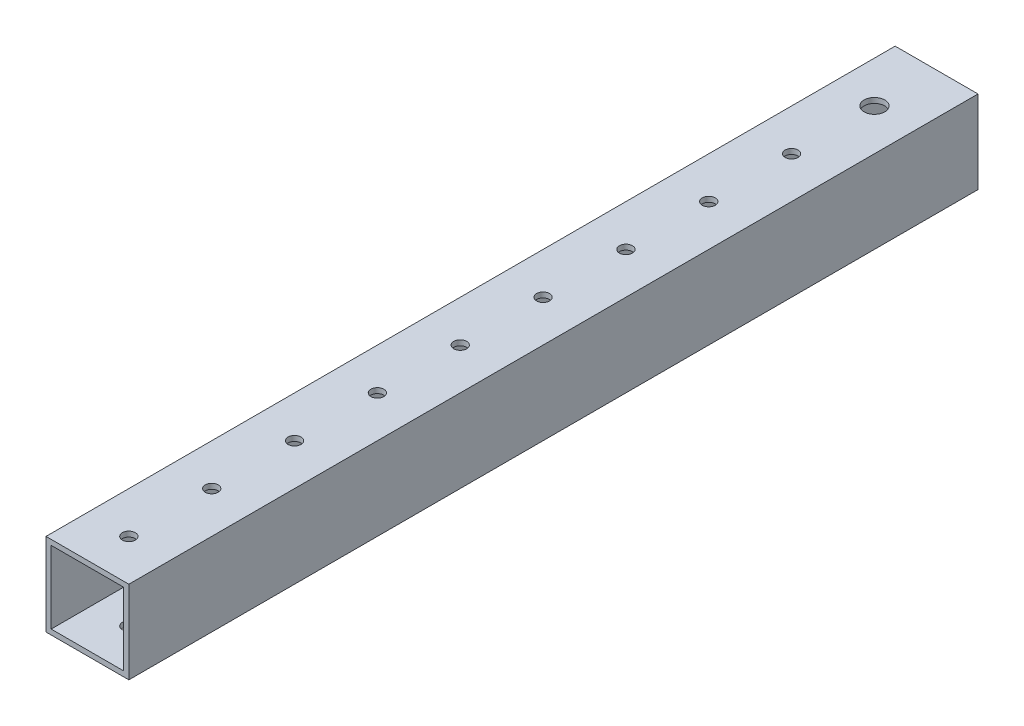
SolidWorks part; units mm, degrees
ref_plane "Front Plane" through (0, 0, 0) normal (0, 0, 1) x (1, 0, 0)
ref_plane "Top Plane" through (0, 0, 0) normal (0, 1, 0) x (1, 0, 0)
ref_plane "Right Plane" through (0, 0, 0) normal (1, 0, 0) x (0, 0, -1)
sketch "Sketch1" plane through (0, 0, 0) normal (0, 0, 1) x (1, 0, 0)
  line L1 (-11.1125, 11.1125) -> (11.1125, 11.1125)
  line L2 (-11.1125, 11.1125) -> (-11.1125, -11.1125)
  line L3 (-11.1125, -11.1125) -> (11.1125, -11.1125)
  line L4 (11.1125, 11.1125) -> (11.1125, -11.1125)
  line L5 (-11.1125, 11.1125) -> (11.1125, -11.1125) construction
  line L6 (-11.1125, -11.1125) -> (11.1125, 11.1125) construction
  line L7 (-12.7, 12.7) -> (12.7, 12.7)
  line L8 (-12.7, 12.7) -> (-12.7, -12.7)
  line L9 (-12.7, -12.7) -> (12.7, -12.7)
  line L10 (12.7, 12.7) -> (12.7, -12.7)
  line L11 (-12.7, 12.7) -> (12.7, -12.7) construction
  line L12 (-12.7, -12.7) -> (12.7, 12.7) construction
  point P0 (0, 0)
  point P6 (0, 0)
  dimension "D1" = 25.4
  dimension "D2" = 25.4
  dimension "D3" = 1.5875
extrude "Boss-Extrude1" add sketch "Sketch1" along normal blind 260.35
sketch "Sketch2" plane through (0, 12.7, 0) normal (0, 1, 0) x (1, 0, 0)
  line L0 (0, -260.35) -> (0, -247.65) construction
  line L1 (12.7, -260.35) -> (-12.7, -260.35) construction
  circle A0 centre (0, -247.65) radius 1.9844
  circle A1 centre (0, -222.25) radius 1.9844
  circle A2 centre (0, -196.85) radius 1.9844
  circle A3 centre (0, -171.45) radius 1.9844
  circle A4 centre (0, -146.05) radius 1.9844
  circle A5 centre (0, -120.65) radius 1.9844
  circle A6 centre (0, -95.25) radius 1.9844
  circle A7 centre (0, -69.85) radius 1.9844
  circle A8 centre (0, -44.45) radius 1.9844
  circle A10 centre (0, 6.35) radius 1.9844
  circle A11 centre (0, 31.75) radius 1.9844
  circle A12 centre (0, -19.05) radius 3.175
  circle A13 centre (0, -19.05) radius 1.9844 [skipped]
  dimension "D2" = 3.9688
  dimension "D4" = 6.35
  dimension "D1" = 12.7
  dimension "D3" = 12
extrude "Cut-Extrude1" cut sketch "Sketch2" against normal through all
